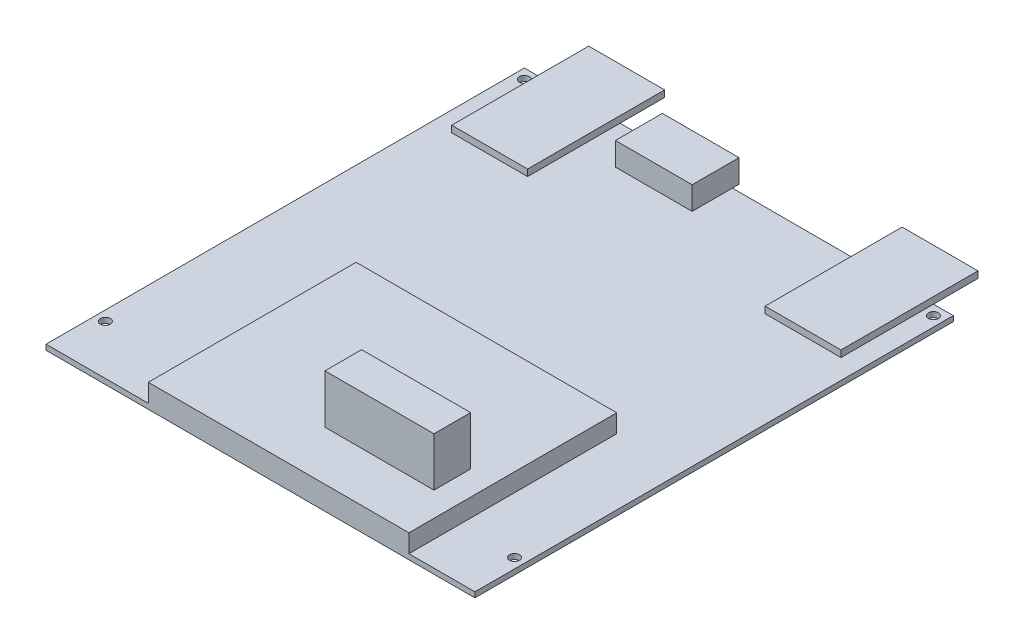
SolidWorks part; units mm, degrees
ref_plane "Plan de face" through (0, 0, 0) normal (0, 0, 1) x (1, 0, 0)
ref_plane "Plan de dessus" through (0, 0, 0) normal (0, 1, 0) x (1, 0, 0)
ref_plane "Plan de droite" through (0, 0, 0) normal (1, 0, 0) x (0, 0, -1)
sketch "Esquisse1" plane through (0, 0, 0) normal (0, 1, 0) x (1, 0, 0)
  line L0 (0, 0) -> (0, 174.1389) construction
  line L1 (-65, 145) -> (65, 145)
  line L2 (-65, 145) -> (-65, 0)
  line L3 (-65, 0) -> (65, 0)
  line L4 (65, 145) -> (65, 0)
  circle A0 centre (-62, 142) radius 1.5
  circle A1 centre (62, 142) radius 1.5
  circle A2 centre (62, 15) radius 1.5
  circle A3 centre (-62, 15) radius 1.5
  dimension "D6" = 3
  dimension "D1" = 145
  dimension "D2" = 130
  dimension "D3" = 15
  dimension "D4" = 3
  dimension "D5" = 3
extrude "Boss.-Extru.1" add sketch "Esquisse1" along normal blind 1.6
sketch "Esquisse2" plane through (0, 1.6, 0) normal (0, 1, 0) x (1, 0, 0)
  line L0 (-65, 0) -> (65, 0) construction
  line L1 (-34, 0) -> (45, 0)
  line L2 (-34, 0) -> (-34, 63)
  line L3 (-34, 63) -> (45, 63)
  line L4 (45, 0) -> (45, 63)
  line L5 (-65, 145) -> (-65, 0) construction
  dimension "D1" = 79
  dimension "D2" = 63
  dimension "D3" = 31
extrude "Boss.-Extru.2" add sketch "Esquisse2" along normal blind 5.5
sketch "Esquisse3" plane through (0, 7.1, 0) normal (0, 1, 0) x (1, 0, 0)
  line L1 (4.5658, 26.0922) -> (37.613, 26.0922)
  line L2 (4.5658, 26.0922) -> (4.5658, 14.9843)
  line L3 (4.5658, 14.9843) -> (37.613, 14.9843)
  line L4 (37.613, 26.0922) -> (37.613, 14.9843)
extrude "Boss.-Extru.3" add sketch "Esquisse3" along normal blind 14.8
sketch "Esquisse4" plane through (0, 1.6, 0) normal (0, 1, 0) x (1, 0, 0)
  line L0 (65, 145) -> (-65, 145) construction
  line L1 (-25.1794, 147) -> (-1.9397, 147)
  line L2 (-25.1794, 147) -> (-25.1794, 132.7834)
  line L3 (-25.1794, 132.7834) -> (-1.9397, 132.7834)
  line L4 (-1.9397, 147) -> (-1.9397, 132.7834)
  dimension "D1" = 2
extrude "Boss.-Extru.4" add sketch "Esquisse4" along normal blind 7
sketch "Esquisse5" plane through (0, 1.6, 0) normal (0, 1, 0) x (1, 0, 0)
  line L0 (0, 0) -> (0, 186.2703) construction
  line L1 (-59, 158.5) -> (-36, 158.5)
  line L2 (-59, 158.5) -> (-59, 116.9741)
  line L3 (-59, 116.9741) -> (-36, 116.9741)
  line L4 (-36, 158.5) -> (-36, 116.9741)
  line L5 (36, 158.5) -> (36, 116.9741)
  line L6 (59, 116.9741) -> (36, 116.9741)
  line L7 (59, 158.5) -> (59, 116.9741)
  line L8 (59, 158.5) -> (36, 158.5)
  line L9 (-25.1794, 145) -> (-65, 145) construction
  line L10 (-65, 145) -> (-65, 0) construction
  dimension "D1" = 13.5
  dimension "D2" = 23
  dimension "D3" = 6
extrude "Boss.-Extru.5" add sketch "Esquisse5" along normal blind 2
sketch "Esquisse6" plane through (0, 0, 0) normal (0, -1, 0) x (1, 0, 0)
  line L0 (0, 0) -> (0, -130.5884) construction
  line L1 (23.6692, -104.496) -> (17.4583, -104.496)
  line L2 (23.6692, -104.496) -> (23.6692, -58.3055)
  line L3 (23.6692, -58.3055) -> (17.4583, -58.3055)
  line L4 (17.4583, -104.496) -> (17.4583, -58.3055)
  line L5 (-17.4583, -104.496) -> (-17.4583, -58.3055)
  line L6 (-23.6692, -58.3055) -> (-17.4583, -58.3055)
  line L7 (-23.6692, -104.496) -> (-23.6692, -58.3055)
  line L8 (-23.6692, -104.496) -> (-17.4583, -104.496)
extrude "Boss.-Extru.6" add sketch "Esquisse6" along normal blind 17.7
sketch "Esquisse7" plane through (0, -17.7, 0) normal (0, -1, 0) x (1, 0, 0)
  line L0 (65, -145) -> (-65, -145) construction
  line L1 (34.25, -145) -> (-34.25, -145)
  line L2 (34.25, -145) -> (34.25, -49)
  line L3 (34.25, -49) -> (-34.25, -49)
  line L4 (-34.25, -145) -> (-34.25, -49)
  line L5 (0, 0) -> (0, -94.4905) construction
  dimension "D1" = 68.5
  dimension "D2" = 96
extrude "Boss.-Extru.7" add sketch "Esquisse7" against normal blind 1.6
sketch "Esquisse8" plane through (0, -16.1, 0) normal (0, 1, 0) x (1, 0, 0)
  line L0 (-34.25, 145) -> (34.25, 145) construction
  line L1 (-22.6838, 134.6506) -> (-27.91, 134.6506)
  line L2 (-22.6838, 134.6506) -> (-22.6838, 161)
  line L3 (-22.6838, 161) -> (-27.91, 161)
  line L4 (-27.91, 134.6506) -> (-27.91, 161)
  dimension "D1" = 16
extrude "Boss.-Extru.8" add sketch "Esquisse8" along normal blind 5
